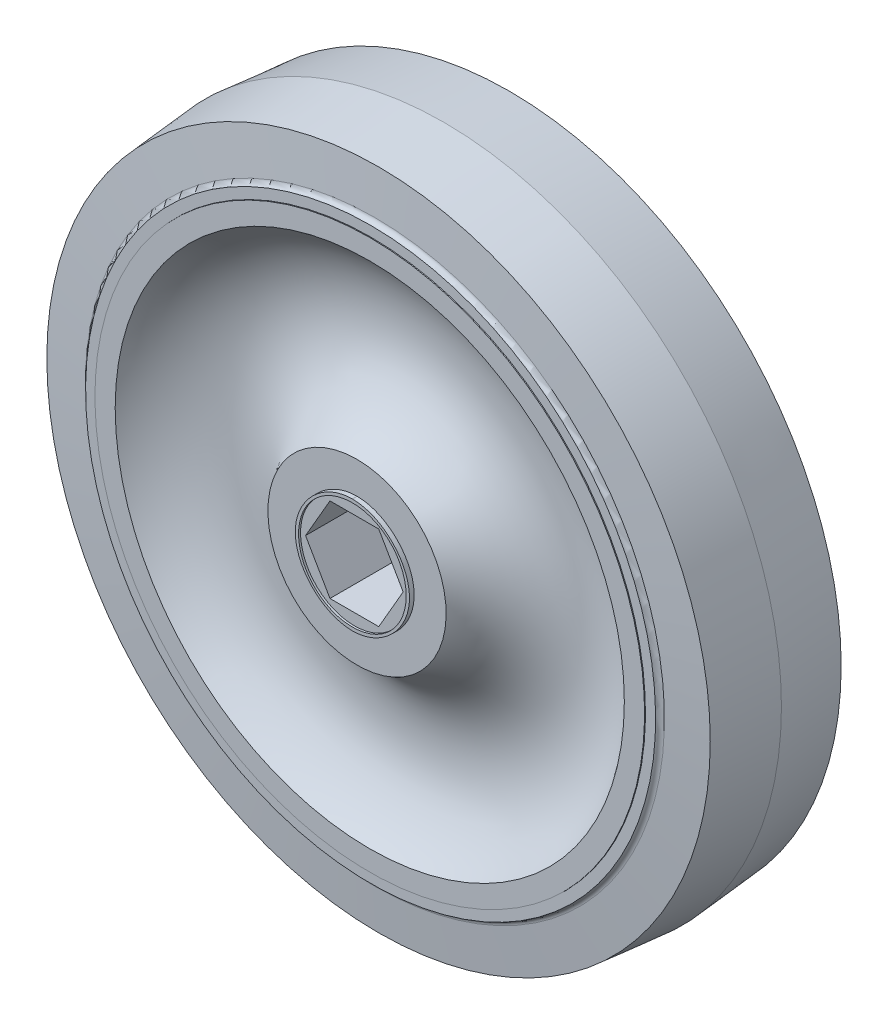
SolidWorks part; units mm, degrees
ref_plane "Front Plane" through (0, 0, 0) normal (0, 0, 1) x (1, 0, 0)
ref_plane "Top Plane" through (0, 0, 0) normal (0, 1, 0) x (1, 0, 0)
ref_plane "Right Plane" through (0, 0, 0) normal (1, 0, 0) x (0, 0, -1)
ref_plane "Plane1" through (0, 0, 0) normal (0, -1, 0) x (1, 0, 0)
sketch "Sketch1" plane through (0, 0, 0) normal (0, -1, 0) x (1, 0, 0)
  line L0 (13.4159, 13.0937) -> (0, 13.0937)
  line L1 (0, 13.0937) -> (0, -13.0937)
  line L2 (0, -13.0937) -> (13.4159, -13.0937)
  line L3 (38.3246, -11.176) -> (41.3737, -11.176)
  line L4 (41.3737, -11.176) -> (41.6266, -6.3499)
  line L5 (41.6306, -6.35) -> (41.3843, -11.049)
  line L6 (41.3843, -11.049) -> (42.9083, -11.049)
  line L7 (43.5945, -10.4094) -> (49.9378, -9.8544)
  line L8 (49.9378, -9.8544) -> (50.8, 0)
  line L9 (50.8, 0) -> (49.9378, 9.8544)
  line L10 (49.9378, 9.8544) -> (43.5945, 10.4094)
  line L11 (42.9083, 11.049) -> (41.3843, 11.049)
  line L12 (41.3843, 11.049) -> (41.6306, 6.3501)
  line L13 (41.6266, 6.35) -> (41.3737, 11.176)
  line L14 (41.3737, 11.176) -> (38.3246, 11.176)
  line L15 (0, 13.0937) -> (0, -13.0937) construction
  line L16 (41.6266, 6.35) -> (41.6306, 6.3501)
  line L17 (41.6266, -6.3499) -> (41.6306, -6.35)
  arc A0 (13.4159, -13.0937) -> (38.3246, -11.176) centre (26.4026, -19.05) cw
  arc A1 (42.9083, -11.049) -> (43.5945, -10.4094) centre (43.6609, -11.1685) cw
  arc A2 (43.5945, 10.4094) -> (42.9083, 11.049) centre (43.6609, 11.1685) cw
  arc A3 (38.3246, 11.176) -> (13.4159, 13.0937) centre (26.4026, 19.05) cw
revolve "Revolve1" add sketch "Sketch1" angle 360 about L15
ref_plane "Plane2" through (0, 0, 13.0937) normal (0, 0, -1) x (-1, 0, 0)
sketch "Sketch2" plane through (0, 0, 13.0937) normal (0, 0, -1) x (-1, 0, 0)
  spline S0 degree 3 poles (0, -8.6035) (-4.5048, -8.6035) (-8.6035, -4.5048) (-8.6035, 4.5048) (-4.5048, 8.6035) (0, 8.6035) knots 0 0 0 0 0.5 0.5 1 1 1 1
  spline S1 degree 3 poles (0, 8.6035) (4.5048, 8.6035) (8.6035, 4.5048) (8.6035, -4.5048) (4.5048, -8.6035) (0, -8.6035) knots 0 0 0 0 0.5 0.5 1 1 1 1
extrude "Boss-Extrude1" add sketch "Sketch2" against normal blind 0.7001 draft 0.5
ref_plane "Plane3" through (0, 0, -13.0937) normal (0, 0, 1) x (1, 0, 0)
sketch "Sketch3" plane through (0, 0, -13.0937) normal (0, 0, 1) x (1, 0, 0)
  circle A0 centre (0, 0) radius 8.6035
extrude "Boss-Extrude2" add sketch "Sketch3" against normal blind 0.7001 draft 0.5
hole_wizard "Hole1" positions "Sketch5" profile "Sketch4" legacy
sketch "Sketch5" plane through (0, 0, 13.7937) normal (0, 0, 1) x (1, 0, 0)
  point P0 (0, 0)
sketch "Sketch4" plane through (0, 0, 13.7937) normal (1, 0, 0) x (0, -1, 0)
  line L0 (0, 0) -> (0, 0.3)
  line L1 (0, 0.3) -> (8.1, 0.3)
  line L2 (8.1, 0.3) -> (8.1026, 0)
  line L3 (8.1026, 0) -> (0, 0)
  line L4 (0, 110) -> (0, -10) construction
  dimension "Minor Diameter" = 16.2
  dimension "Depth" = 0.3
  dimension "Major Diameter" = 16.2052
hole_wizard "Hole2" positions "Sketch7" profile "Sketch6" legacy
sketch "Sketch7" plane through (0, 0, -13.7937) normal (0, 0, -1) x (-1, 0, 0)
  point P0 (0, 0)
sketch "Sketch6" plane through (0, 0, -13.7937) normal (1, 0, 0) x (0, 1, 0)
  line L0 (0, 0) -> (0, 0.3)
  line L1 (0, 0.3) -> (8.1, 0.3)
  line L2 (8.1, 0.3) -> (8.1026, 0)
  line L3 (8.1026, 0) -> (0, 0)
  line L4 (0, 110) -> (0, -10) construction
  dimension "Minor Diameter" = 16.2
  dimension "Depth" = 0.3
  dimension "Major Diameter" = 16.2052
sketch "Sketch8" plane through (0, 0, -13.4937) normal (0, 0, -1) x (-1, 0, 0)
  line L0 (-7.347, 0) -> (-3.6735, -6.3627)
  line L1 (-3.6735, -6.3627) -> (3.6735, -6.3627)
  line L2 (3.6735, -6.3627) -> (7.347, 0)
  line L3 (7.347, 0) -> (3.6735, 6.3627)
  line L4 (3.6735, 6.3627) -> (-3.6735, 6.3627)
  line L5 (-3.6735, 6.3627) -> (-7.347, 0)
extrude "Cut-Extrude1" cut sketch "Sketch8" against normal up to next
chamfer "Chamfer1" distance 0.3 angle 45 6 edges at (-5.5103, -3.1814, -13.4937) (0, -6.3627, -13.4937) (-5.5103, 3.1813, -13.4937) (5.5103, -3.1813, -13.4937) (0, 6.3627, -13.4937) (5.5103, 3.1814, -13.4937)
